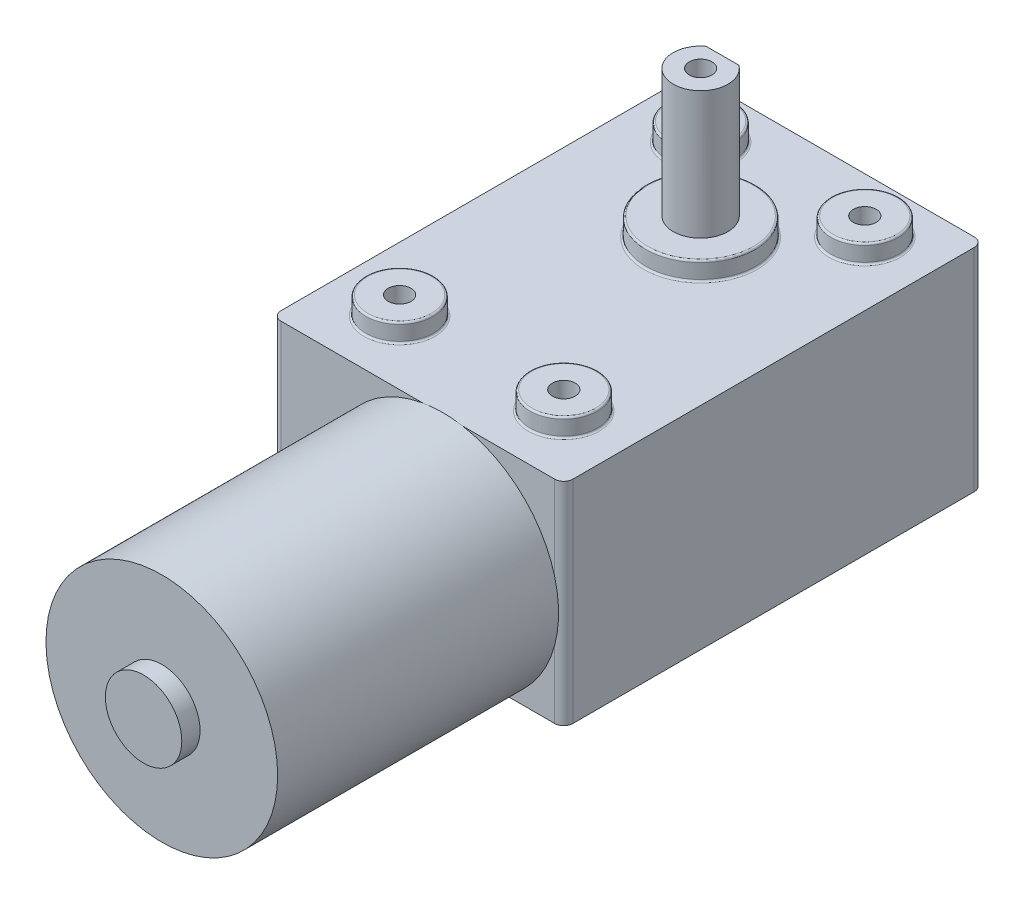
SolidWorks part; units mm, degrees
ref_plane "Front Plane" through (0, 0, 0) normal (0, 0, 1) x (1, 0, 0)
ref_plane "Top Plane" through (0, 0, 0) normal (0, 1, 0) x (1, 0, 0)
ref_plane "Right Plane" through (0, 0, 0) normal (1, 0, 0) x (0, 0, -1)
sketch "Sketch1" plane through (0, 0, 0) normal (0, 1, 0) x (1, 0, 0)
  line L1 (0, 0) -> (32, 0)
  line L2 (0, 0) -> (0, 46)
  line L3 (0, 46) -> (32, 46)
  line L4 (32, 0) -> (32, 46)
  dimension "D1" = 46
  dimension "D2" = 32
extrude "Boss-Extrude1" add sketch "Sketch1" along normal blind 23.2
sketch "Sketch2" plane through (0, 23.2, 0) normal (0, 1, 0) x (1, 0, 0)
  line L0 (32, 46) -> (0, 46) construction
  line L1 (7, 40) -> (25, 40) construction
  line L2 (7, 40) -> (7, 7) construction
  line L3 (7, 7) -> (25, 7) construction
  line L4 (25, 40) -> (25, 7) construction
  line L6 (16, 46) -> (16, 0) construction
  line L7 (0, 0) -> (32, 0) construction
  circle A0 centre (7, 40) radius 3.7
  circle A1 centre (25, 40) radius 3.7
  circle A2 centre (7, 7) radius 3.7
  circle A3 centre (25, 7) radius 3.7
  circle A4 centre (16, 31) radius 6
  point P10 (16, 40)
  dimension "D4" = 7.4
  dimension "D5" = 12
  dimension "D1" = 6
  dimension "D2" = 7
  dimension "D3" = 18
  dimension "D6" = 15
extrude "Boss-Extrude2" add sketch "Sketch2" along normal blind 2
sketch "Sketch8" plane through (0, 25.2, 0) normal (0, 1, 0) x (1, 0, 0)
  circle A0 centre (16, 31) radius 3
  circle A1 centre (16, 31) radius 6
  circle A2 centre (16, 31) radius 6 construction
  dimension "D2" = 6
  dimension "D1" = 0
extrude "Boss-Extrude3" add sketch "Sketch8" along normal blind 14
sketch "Sketch14" plane through (0, 39.2, 0) normal (0, 1, 0) x (1, 0, 0)
  circle A1 centre (16, 31) radius 3
  circle A2 centre (16, 31) radius 3 construction
  dimension "D1" = 0
hole_wizard "M3x0.5 Tapped Hole2" positions "Sketch15" profile "Sketch16" tap size "M3x0.5" standard "ANSI Metric"
sketch "Sketch15" plane through (0, 39.2, 0) normal (0, 1, 0) x (1, 0, 0)
  point P0 (16, 31)
sketch "Sketch16" plane through (16, 39.2, -31) normal (1, 0, 0) x (0, 0, 1)
  line L0 (0, 0) -> (0, 12.7511)
  line L1 (0, 12.7511) -> (1.25, 12)
  line L2 (1.25, 12) -> (1.25, 0)
  line L5 (1.25, 0) -> (0, 0)
  line L10 (0, 12.7511) -> (-1.25, 12) construction
  line L11 (0, -6.35) -> (0, 107.95) construction
  dimension "Tap Drill Dia." = 2.5
  dimension "Tap Drill Depth" = 12
  dimension "Drill Angle" = 118
cosmetic thread "Hole Thread5" parameters "D1"=6, "D2"=3
sketch "Sketch9" plane through (0, 39.2, 0) normal (0, 1, 0) x (1, 0, 0)
  line L0 (14.2, 33.4) -> (17.8, 33.4)
  arc A1 (14.2, 33.4) -> (17.8, 33.4) centre (16, 31) cw
  circle A2 centre (16, 31) radius 3
  circle A3 centre (16, 31) radius 3 construction
  point P2 (16, 34)
  dimension "D2" = 0.6
  dimension "D1" = 0
extrude "Cut-Extrude1" cut sketch "Sketch9" against normal blind 12
sketch "Sketch5" plane through (0, 25.2, 0) normal (0, 1, 0) x (1, 0, 0)
  circle A0 centre (7, 40) radius 3.7 construction
  circle A1 centre (7, 40) radius 3.7
  circle A2 centre (25, 40) radius 3.7 construction
  circle A3 centre (25, 40) radius 3.7
  circle A4 centre (7, 7) radius 3.7 construction
  circle A5 centre (7, 7) radius 3.7
  circle A6 centre (25, 7) radius 3.7 construction
  circle A7 centre (25, 7) radius 3.7
hole_wizard "M3x0.5 Tapped Hole1" positions "Sketch6" profile "Sketch7" tap size "M3x0.5" standard "ANSI Metric"
sketch "Sketch6" plane through (0, 25.2, 0) normal (0, 1, 0) x (1, 0, 0)
  point P0 (25, 7)
  point P3 (7, 7)
  point P6 (7, 40)
  point P9 (25, 40)
sketch "Sketch7" plane through (25, 25.2, -7) normal (1, 0, 0) x (0, 0, 1)
  line L0 (0, 0) -> (0, 8.2511)
  line L1 (0, 8.2511) -> (1.25, 7.5)
  line L2 (1.25, 7.5) -> (1.25, 0)
  line L5 (1.25, 0) -> (0, 0)
  line L10 (0, 8.2511) -> (-1.25, 7.5) construction
  line L11 (0, -6.35) -> (0, 107.95) construction
  dimension "Tap Drill Dia." = 2.5
  dimension "Tap Drill Depth" = 7.5
  dimension "Drill Angle" = 118
cosmetic thread "Hole Thread1" parameters "D1"=6, "D2"=3
cosmetic thread "Hole Thread2" parameters "D1"=6, "D2"=3
cosmetic thread "Hole Thread3" parameters "D1"=6, "D2"=3
cosmetic thread "Hole Thread4" parameters "D1"=6, "D2"=3
fillet "Fillet1" radius 1 4 edges at (0, 11.6, -46) (0, 11.6, 0) (32, 11.6, -46) (32, 11.6, 0)
fillet "Fillet2" radius 0.2 10 edges at (7, 25.2, -36.3) (25, 25.2, -36.3) (25, 25.2, -3.3) (7, 25.2, -3.3) (7, 23.2, -43.7) (25, 23.2, -43.7) (7, 23.2, -10.7) (25, 23.2, -10.7) (16, 25.2, -25) (16, 23.2, -37)
sketch "Sketch11" plane through (-0.759, 0, 0) normal (0, 0, 1) x (1, 0, 0)
  circle A0 centre (19.4888, 10.6882) radius 12.7
  dimension "D1" = 25.4
extrude "Boss-Extrude4" add sketch "Sketch11" along normal blind 30.8
sketch "Sketch17" plane through (-0.759, 0, 30.8) normal (0, 0, 1) x (1, 0, 0)
  circle A0 centre (19.4888, 10.6882) radius 4.1891
  circle A1 centre (19.4888, 10.6882) radius 12.7
  circle A2 centre (19.4888, 10.6882) radius 12.7 construction
  dimension "D1" = 0
extrude "Boss-Extrude5" add sketch "Sketch17" along normal blind 2
